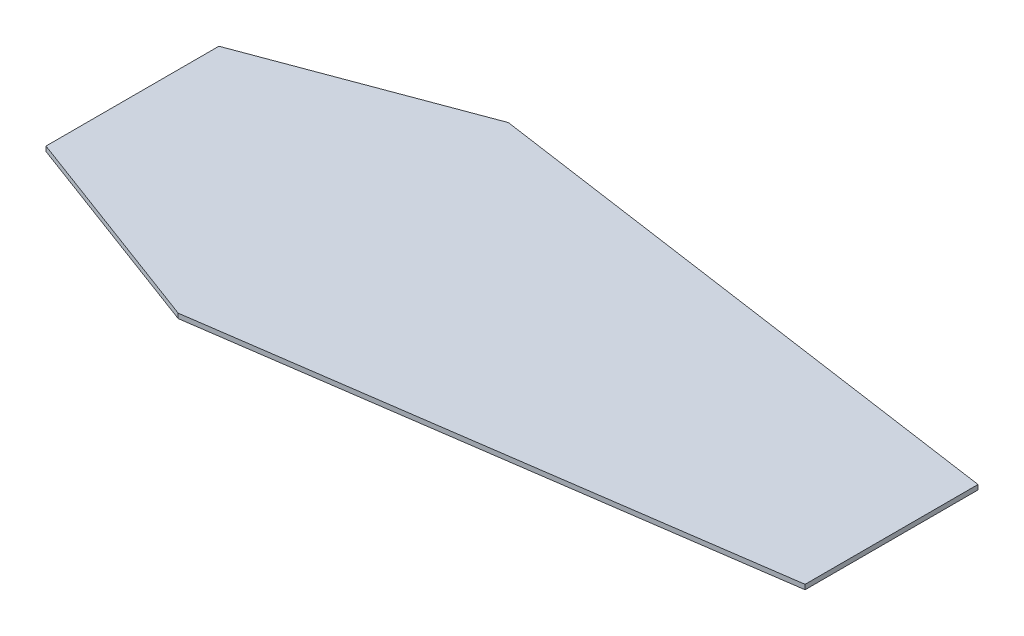
SolidWorks part; units mm, degrees
ref_plane "Front Plane" through (0, 0, 0) normal (0, 0, 1) x (1, 0, 0)
ref_plane "Top Plane" through (0, 0, 0) normal (0, 1, 0) x (1, 0, 0)
ref_plane "Right Plane" through (0, 0, 0) normal (1, 0, 0) x (0, 0, -1)
sketch "Sketch1" plane through (0, 0, 0) normal (0, 1, 0) x (1, 0, 0)
  line L0 (-1317.7068, 355.8791) -> (-1317.7068, -164.8209)
  line L1 (968.2932, 355.8791) -> (968.2932, -164.8209)
  line L2 (-682.7068, 592.6071) -> (968.2932, 355.8791)
  line L3 (-682.7068, -401.5648) -> (968.2932, -164.8209)
  line L4 (-682.7068, 592.6071) -> (-1317.7068, 355.8791)
  line L5 (-1317.7068, -164.8209) -> (-682.7068, -401.5648)
  line L6 (-1317.7068, 95.5291) -> (968.2932, 95.5291) construction
  line L7 (-682.7068, 592.6071) -> (-682.7068, -401.5648) construction
  dimension "D1" = 520.7
  dimension "D2" = 677.6966
  dimension "D3" = 1667.8875
  dimension "D4" = 520.7
  dimension "D5" = 1667.8852
  dimension "D6" = 677.691
extrude "Boss-Extrude1" add sketch "Sketch1" along normal blind 14.2875
sketch "Sketch2" plane through (0, 14.2875, 0) normal (0, 1, 0) x (1, 0, 0)
  line L0 (-1317.7068, 95.5291) -> (968.2932, 95.5291) construction
  line L1 (-1317.7068, 355.8791) -> (-1317.7068, -164.8209) construction
  line L2 (968.2932, -164.8209) -> (968.2932, 355.8791) construction
  line L3 (-682.7068, 592.6071) -> (-682.7068, -401.5648) construction
sketch "Sketch3" plane through (968.2932, 0, 0) normal (1, 0, 0) x (0, 0, -1)
  line L0 (95.5291, 14.2875) -> (95.5291, 0) construction
  line L1 (-164.8209, 14.2875) -> (355.8791, 14.2875) construction
  line L2 (-164.8209, 0) -> (355.8791, 0) construction
  line L3 (-164.8209, 7.1437) -> (355.8791, 7.1437) construction
  line L4 (-164.8209, 14.2875) -> (-164.8209, 0) construction
  line L5 (355.8791, 14.2875) -> (355.8791, 0) construction
